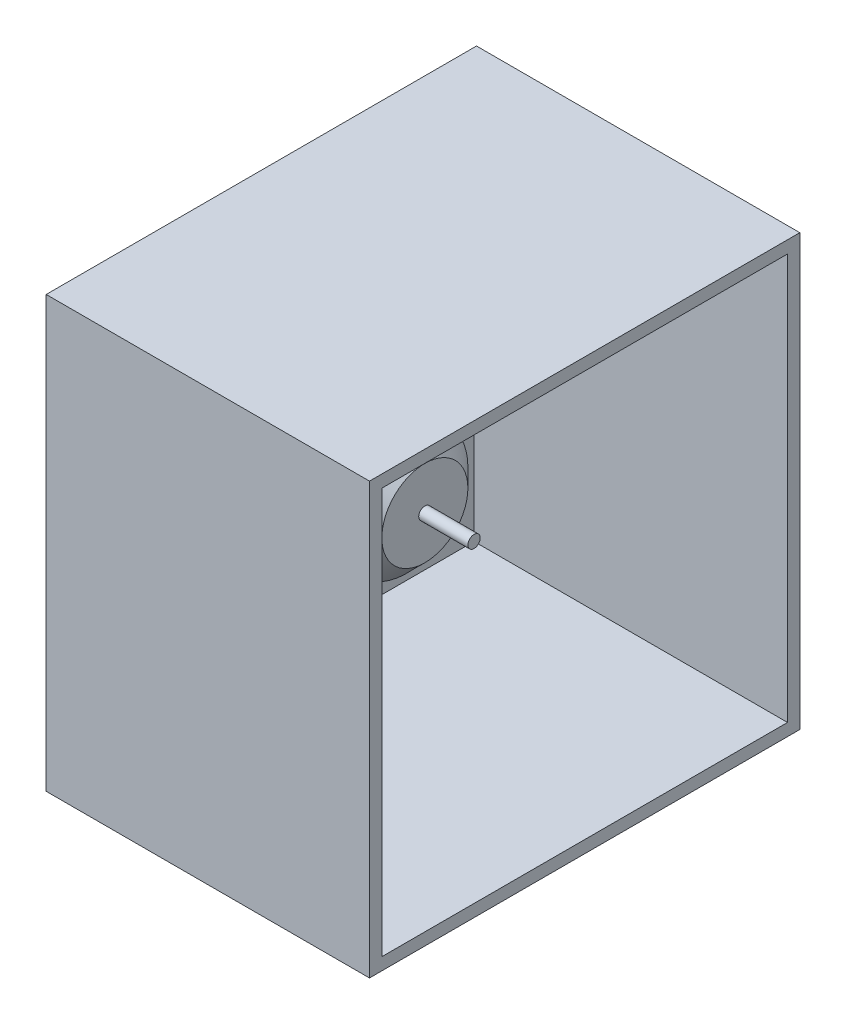
SolidWorks part; units mm, degrees
ref_plane "Front Plane" through (0, 0, 0) normal (0, 0, 1) x (1, 0, 0)
ref_plane "Top Plane" through (0, 0, 0) normal (0, 1, 0) x (1, 0, 0)
ref_plane "Right Plane" through (0, 0, 0) normal (1, 0, 0) x (0, 0, -1)
sketch "Sketch1" plane through (0, 0, 0) normal (1, 0, 0) x (0, 0, -1)
  circle A0 centre (0, 0) radius 12.7
  dimension "D1" = 25.4
extrude "Boss-Extrude1" add sketch "Sketch1" along normal mid plane 30.48
chamfer "Chamfer1" distance 3.81 angle 45 1 edges at (15.24, 0, -12.7)
chamfer "Chamfer3" distance 5.08 angle 30 1 edges at (-15.24, 0, -12.7)
sketch "Sketch2" plane through (15.24, 0, 0) normal (1, 0, 0) x (0, 0, -1)
  circle A0 centre (0, 0) radius 1.27
  dimension "D1" = 2.54
extrude "Boss-Extrude3" add sketch "Sketch2" along normal blind 10.16
sketch "Sketch3" plane through (-15.24, 0, 0) normal (-1, 0, 0) x (0, 0, 1)
  line L0 (-5.715, -1.905) -> (-17.78, -1.905)
  line L1 (-0.635, -19.05) -> (0.635, -19.05)
  line L2 (-1.905, -17.78) -> (-1.905, -5.715)
  line L3 (-0.635, 19.05) -> (0.635, 19.05)
  line L4 (1.905, -17.78) -> (1.905, -5.715)
  line L5 (-1.905, -19.05) -> (1.905, 19.05) construction
  line L6 (-1.905, 19.05) -> (1.905, -19.05) construction
  line L7 (17.78, 1.905) -> (5.715, 1.905)
  line L8 (19.05, 0.635) -> (19.05, -0.635)
  line L9 (17.78, -1.905) -> (5.715, -1.905)
  line L10 (-19.05, 0.635) -> (-19.05, -0.635)
  line L11 (19.05, 1.905) -> (-19.05, -1.905) construction
  line L12 (19.05, -1.905) -> (-19.05, 1.905) construction
  line L13 (-5.715, 1.905) -> (-17.78, 1.905)
  line L14 (-1.905, 5.715) -> (-1.905, 17.78)
  line L15 (1.905, 5.715) -> (1.905, 17.78)
  line L16 (-19.05, 0) -> (19.05, 0) construction
  line L17 (0, 19.05) -> (0, -19.05) construction
  line L18 (17.78, -0.635) -> (17.78, 0.635) construction
  line L19 (-17.78, -0.635) -> (-17.78, 0.635) construction
  line L20 (0.635, 17.78) -> (-0.635, 17.78) construction
  line L21 (0.635, -17.78) -> (-0.635, -17.78) construction
  arc A0 (5.715, -1.905) -> (1.905, -5.715) centre (5.715, -5.715) ccw
  arc A1 (5.715, 1.905) -> (1.905, 5.715) centre (5.715, 5.715) cw
  arc A2 (-1.905, 5.715) -> (-5.715, 1.905) centre (-5.715, 5.715) cw
  arc A3 (-5.715, -1.905) -> (-1.905, -5.715) centre (-5.715, -5.715) cw
  arc A4 (17.78, 1.905) -> (19.05, 0.635) centre (17.78, 0.635) cw
  arc A5 (19.05, -0.635) -> (17.78, -1.905) centre (17.78, -0.635) cw
  arc A6 (0.635, -19.05) -> (1.905, -17.78) centre (0.635, -17.78) ccw
  arc A7 (-0.635, -19.05) -> (-1.905, -17.78) centre (-0.635, -17.78) cw
  arc A8 (-17.78, -1.905) -> (-19.05, -0.635) centre (-17.78, -0.635) cw
  arc A9 (-17.78, 1.905) -> (-19.05, 0.635) centre (-17.78, 0.635) ccw
  arc A10 (0.635, 19.05) -> (1.905, 17.78) centre (0.635, 17.78) cw
  arc A11 (-1.905, 17.78) -> (-0.635, 19.05) centre (-0.635, 17.78) cw
  circle A12 centre (0, -17.78) radius 0.6399
  circle A13 centre (17.78, 0) radius 0.635
  circle A14 centre (0, 17.78) radius 0.635
  circle A15 centre (-17.78, 0) radius 0.635
  point P0 (0, 0)
  point P6 (0, 0)
  point P19 (1.905, 1.905)
  point P22 (-1.905, 1.905)
  dimension "D5" = 3.81
  dimension "D6" = 1.27
  dimension "D1" = 38.1
  dimension "D2" = 38.1
  dimension "D3" = 3.81
  dimension "D4" = 3.81
extrude "Boss-Extrude5" add sketch "Sketch3" along normal blind 1.27
sketch "Sketch4" plane through (-16.51, 0, 0) normal (-1, 0, 0) x (0, 0, 1)
  line L1 (-44.45, 44.45) -> (44.45, 44.45)
  line L2 (-44.45, 44.45) -> (-44.45, -44.45)
  line L3 (-44.45, -44.45) -> (44.45, -44.45)
  line L4 (44.45, 44.45) -> (44.45, -44.45)
  line L5 (-44.45, 44.45) -> (44.45, -44.45) construction
  line L6 (-44.45, -44.45) -> (44.45, 44.45) construction
  point P0 (0, 0)
  dimension "D1" = 88.9
  dimension "D2" = 88.9
extrude "Boss-Extrude6" add sketch "Sketch4" along normal blind 2.032
sketch "Sketch5" plane through (-18.542, 0, 0) normal (-1, 0, 0) x (0, 0, 1)
  line L0 (0, 0) -> (0, 29.21) construction
  line L1 (0, 0) -> (29.21, 0) construction
  circle A0 centre (0, 0) radius 29.21 construction
  circle A1 centre (0, 29.21) radius 3.81
  circle A2 centre (20.6546, 20.6546) radius 3.81
  circle A3 centre (29.21, 0) radius 3.81
  circle A4 centre (20.6546, -20.6546) radius 3.81
  circle A5 centre (0, -29.21) radius 3.81
  circle A6 centre (-20.6546, -20.6546) radius 3.81
  circle A7 centre (-29.21, 0) radius 3.81
  circle A8 centre (-20.6546, 20.6546) radius 3.81
  point P22 (0, 0)
  dimension "D1" = 58.42
  dimension "D2" = 7.62
  dimension "D4" = 29.21
  dimension "D3" = 8
extrude "Cut-Extrude2" cut sketch "Sketch5" against normal through all
sketch "Sketch7" plane through (-18.542, 0, 0) normal (-1, 0, 0) x (0, 0, 1)
  line L0 (1.905, 5.715) -> (1.905, 7.378) construction
  line L1 (1.905, 7.378) -> (1.905, 17.78) construction
  line L2 (0.635, 19.05) -> (-0.635, 19.05) construction
  line L3 (-1.905, 17.78) -> (-1.905, 5.715) construction
  line L4 (-5.715, 1.905) -> (-7.378, 1.905) construction
  line L5 (-7.378, 1.905) -> (-17.78, 1.905) construction
  line L6 (-19.05, 0.635) -> (-19.05, -0.635) construction
  line L7 (-17.78, -1.905) -> (-7.378, -1.905) construction
  line L8 (-7.378, -1.905) -> (-5.715, -1.905) construction
  line L9 (-1.905, -5.715) -> (-1.905, -7.378) construction
  line L10 (-1.905, -7.378) -> (-1.905, -17.78) construction
  line L11 (1.905, -17.78) -> (1.905, -7.378) construction
  line L12 (7.378, -1.905) -> (17.78, -1.905) construction
  line L13 (17.78, 1.905) -> (7.378, 1.905) construction
  line L14 (7.378, 1.905) -> (5.715, 1.905) construction
  line L15 (19.05, -0.635) -> (19.05, 0.635) construction
  line L16 (-0.635, -19.05) -> (0.635, -19.05) construction
  line L17 (1.905, -7.378) -> (1.905, -5.715) construction
  line L18 (5.715, -1.905) -> (7.378, -1.905) construction
  line L19 (1.905, 5.715) -> (1.905, 7.378)
  line L20 (1.905, 7.378) -> (1.905, 17.78)
  line L21 (0.635, 19.05) -> (-0.635, 19.05)
  line L22 (-1.905, 17.78) -> (-1.905, 5.715)
  line L23 (-5.715, 1.905) -> (-7.378, 1.905)
  line L24 (-7.378, 1.905) -> (-17.78, 1.905)
  line L25 (-19.05, 0.635) -> (-19.05, -0.635)
  line L26 (-17.78, -1.905) -> (-7.378, -1.905)
  line L27 (-7.378, -1.905) -> (-5.715, -1.905)
  line L28 (-1.905, -5.715) -> (-1.905, -7.378)
  line L29 (-1.905, -7.378) -> (-1.905, -17.78)
  line L30 (1.905, -17.78) -> (1.905, -7.378)
  line L31 (7.378, -1.905) -> (17.78, -1.905)
  line L32 (17.78, 1.905) -> (7.378, 1.905)
  line L33 (7.378, 1.905) -> (5.715, 1.905)
  line L34 (19.05, -0.635) -> (19.05, 0.635)
  line L35 (-0.635, -19.05) -> (0.635, -19.05)
  line L36 (1.905, -7.378) -> (1.905, -5.715)
  line L37 (5.715, -1.905) -> (7.378, -1.905)
  arc A0 (1.905, 5.715) -> (5.715, 1.905) centre (5.715, 5.715) ccw construction
  arc A1 (1.905, 17.78) -> (0.635, 19.05) centre (0.635, 17.78) ccw construction
  arc A2 (-0.635, 19.05) -> (-1.905, 17.78) centre (-0.635, 17.78) ccw construction
  arc A3 (-5.715, 1.905) -> (-1.905, 5.715) centre (-5.715, 5.715) ccw construction
  arc A4 (-17.78, 1.905) -> (-19.05, 0.635) centre (-17.78, 0.635) ccw construction
  arc A5 (-19.05, -0.635) -> (-17.78, -1.905) centre (-17.78, -0.635) ccw construction
  arc A6 (-1.905, -5.715) -> (-5.715, -1.905) centre (-5.715, -5.715) ccw construction
  arc A7 (19.05, 0.635) -> (17.78, 1.905) centre (17.78, 0.635) ccw construction
  arc A8 (17.78, -1.905) -> (19.05, -0.635) centre (17.78, -0.635) ccw construction
  arc A9 (-1.905, -17.78) -> (-0.635, -19.05) centre (-0.635, -17.78) ccw construction
  arc A10 (0.635, -19.05) -> (1.905, -17.78) centre (0.635, -17.78) ccw construction
  arc A11 (5.715, -1.905) -> (1.905, -5.715) centre (5.715, -5.715) ccw construction
  arc A12 (1.905, 5.715) -> (5.715, 1.905) centre (5.715, 5.715) ccw
  arc A13 (1.905, 17.78) -> (0.635, 19.05) centre (0.635, 17.78) ccw
  arc A14 (-0.635, 19.05) -> (-1.905, 17.78) centre (-0.635, 17.78) ccw
  arc A15 (-5.715, 1.905) -> (-1.905, 5.715) centre (-5.715, 5.715) ccw
  arc A16 (-17.78, 1.905) -> (-19.05, 0.635) centre (-17.78, 0.635) ccw
  arc A17 (-19.05, -0.635) -> (-17.78, -1.905) centre (-17.78, -0.635) ccw
  arc A18 (-1.905, -5.715) -> (-5.715, -1.905) centre (-5.715, -5.715) ccw
  arc A19 (19.05, 0.635) -> (17.78, 1.905) centre (17.78, 0.635) ccw
  arc A20 (17.78, -1.905) -> (19.05, -0.635) centre (17.78, -0.635) ccw
  arc A21 (-1.905, -17.78) -> (-0.635, -19.05) centre (-0.635, -17.78) ccw
  arc A22 (0.635, -19.05) -> (1.905, -17.78) centre (0.635, -17.78) ccw
  arc A23 (5.715, -1.905) -> (1.905, -5.715) centre (5.715, -5.715) ccw
extrude "Boss-Extrude7" add sketch "Sketch7" along normal blind 1.27
sketch "Sketch8" plane through (-19.812, 0, 0) normal (-1, 0, 0) x (0, 0, 1)
  circle A0 centre (0, 17.78) radius 0.635 construction
  circle A1 centre (17.78, 0) radius 0.635 construction
  circle A2 centre (0, -17.78) radius 0.6399 construction
  circle A3 centre (-17.78, 0) radius 0.635 construction
  circle A4 centre (0, 17.78) radius 0.635
  circle A5 centre (17.78, 0) radius 0.635
  circle A6 centre (0, -17.78) radius 0.6399
  circle A7 centre (-17.78, 0) radius 0.635
extrude "Cut-Extrude3" cut sketch "Sketch8" against normal up to surface (1.27 mm away) up to face at (-18.542, 0, 0)
sketch "Sketch9" plane through (-16.51, 0, 0) normal (1, 0, 0) x (0, 0, -1)
  line L0 (-44.45, 44.45) -> (44.45, 44.45) construction
  line L1 (-44.45, -44.45) -> (-44.45, 44.45) construction
  line L2 (44.45, -44.45) -> (-44.45, -44.45) construction
  line L3 (44.45, 44.45) -> (44.45, -44.45) construction
  line L4 (-44.45, 44.45) -> (44.45, 44.45)
  line L5 (-44.45, -44.45) -> (-44.45, 44.45)
  line L6 (44.45, -44.45) -> (-44.45, -44.45)
  line L7 (44.45, 44.45) -> (44.45, -44.45)
  line L8 (-41.91, -41.91) -> (-41.91, 41.91)
  line L9 (-41.91, 41.91) -> (41.91, 41.91)
  line L10 (41.91, 41.91) -> (41.91, -41.91)
  line L11 (41.91, -41.91) -> (-41.91, -41.91)
  dimension "D1" = 2.54
extrude "Boss-Extrude8" add sketch "Sketch9" along normal blind 80
sketch "Sketch11" plane through (0, 0, 44.45) normal (0, 0, 1) x (1, 0, 0)
  line L0 (-18.542, 44.45) -> (63.49, 44.45) construction
  line L1 (63.49, -44.45) -> (48.25, -44.45)
  line L2 (63.49, -44.45) -> (63.49, 44.45)
  line L3 (63.49, 44.45) -> (48.25, 44.45)
  line L4 (48.25, -44.45) -> (48.25, 44.45)
  dimension "D1" = 15.24
extrude "Cut-Extrude4" cut sketch "Sketch11" against normal through all
